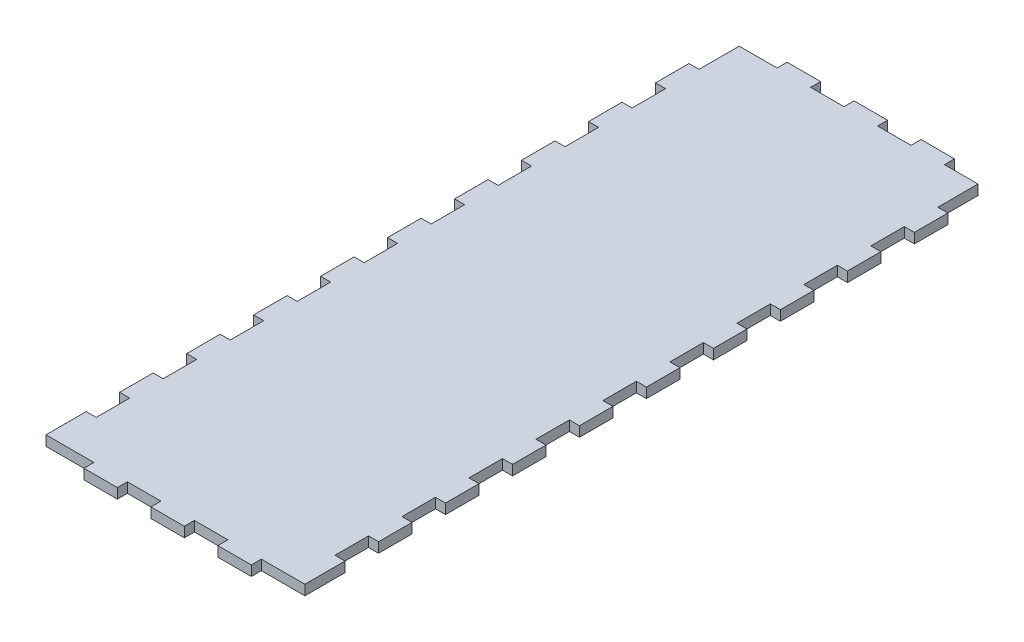
SolidWorks part; units mm, degrees
ref_plane "Front Plane" through (0, 0, 0) normal (0, 0, 1) x (1, 0, 0)
ref_plane "Top Plane" through (0, 0, 0) normal (0, 1, 0) x (1, 0, 0)
ref_plane "Right Plane" through (0, 0, 0) normal (1, 0, 0) x (0, 0, -1)
sketch "Sketch1" plane through (0, 0, 0) normal (0, 1, 0) x (1, 0, 0)
  line L1 (0, 0) -> (35.65, 0)
  line L2 (0, 0) -> (0, 204)
  line L3 (0, 204) -> (35.65, 204)
  line L4 (35.65, 0) -> (35.65, 204)
  dimension "D1" = 35.65
  dimension "D2" = 204
extrude "Boss-Extrude1" add sketch "Sketch1" along normal blind 3
sketch "Sketch2" plane through (35.65, 0, 0) normal (1, 0, 0) x (0, 0, -1)
  line L0 (0, 3) -> (204, 3) construction
  line L1 (0, 0) -> (12, 0)
  line L2 (0, 0) -> (0, 3)
  line L3 (0, 3) -> (12, 3)
  line L4 (12, 0) -> (12, 3)
  line L5 (0, 0) -> (204, 0) construction
  line L6 (22, 0) -> (32, 0)
  line L7 (22, 0) -> (22, 3)
  line L8 (22, 3) -> (32, 3)
  line L9 (32, 0) -> (32, 3)
  line L10 (42, 0) -> (42, 3)
  line L11 (42, 0) -> (52, 0)
  line L12 (52, 0) -> (52, 3)
  line L13 (42, 3) -> (52, 3)
  line L14 (62, 0) -> (62, 3)
  line L15 (62, 0) -> (72, 0)
  line L16 (72, 0) -> (72, 3)
  line L17 (62, 3) -> (72, 3)
  line L18 (82, 0) -> (82, 3)
  line L19 (82, 0) -> (92, 0)
  line L20 (92, 0) -> (92, 3)
  line L21 (82, 3) -> (92, 3)
  line L22 (102, 0) -> (102, 3)
  line L23 (102, 0) -> (112, 0)
  line L24 (112, 0) -> (112, 3)
  line L25 (102, 3) -> (112, 3)
  line L26 (122, 0) -> (122, 3)
  line L27 (122, 0) -> (132, 0)
  line L28 (132, 0) -> (132, 3)
  line L29 (122, 3) -> (132, 3)
  line L30 (142, 0) -> (142, 3)
  line L31 (142, 0) -> (152, 0)
  line L32 (152, 0) -> (152, 3)
  line L33 (142, 3) -> (152, 3)
  line L34 (162, 0) -> (162, 3)
  line L35 (162, 0) -> (172, 0)
  line L36 (172, 0) -> (172, 3)
  line L37 (162, 3) -> (172, 3)
  line L38 (182, 0) -> (182, 3)
  line L39 (182, 0) -> (192, 0)
  line L40 (192, 0) -> (192, 3)
  line L41 (182, 3) -> (192, 3)
  dimension "D1" = 12
  dimension "D2" = 10
  dimension "D3" = 10
  dimension "D4" = 9
extrude "Boss-Extrude2" add sketch "Sketch2" along normal blind 3
mirror "Mirror1" about plane through (0, 0, 0) normal (1, 0, 0) of "Boss-Extrude2", "Boss-Extrude1"
sketch "Esquisse1" plane through (0, 0, -204) normal (0, 0, -1) x (-1, 0, 0)
  line L0 (-35.65, 0) -> (35.65, 0) construction
  line L1 (-25.65, 0) -> (-15.65, 0)
  line L2 (-25.65, 0) -> (-25.65, 3)
  line L3 (-25.65, 3) -> (-15.65, 3)
  line L4 (-15.65, 0) -> (-15.65, 3)
  line L5 (-35.65, 3) -> (35.65, 3) construction
  line L6 (-35.65, 3) -> (-35.65, 0) construction
  line L7 (-5.65, 0) -> (4.35, 0)
  line L8 (-5.65, 0) -> (-5.65, 3)
  line L9 (-5.65, 3) -> (4.35, 3)
  line L10 (4.35, 0) -> (4.35, 3)
  line L11 (14.35, 0) -> (24.35, 0)
  line L12 (14.35, 0) -> (14.35, 3)
  line L13 (14.35, 3) -> (24.35, 3)
  line L14 (24.35, 0) -> (24.35, 3)
  dimension "D1" = 10
  dimension "D2" = 10
  dimension "D4" = 10
  dimension "D3" = 3
extrude "Boss.-Extru.1" add sketch "Esquisse1" along normal blind 3
sketch "Esquisse2" plane through (0, 0, 0) normal (0, 0, 1) x (1, 0, 0)
  line L0 (-38.65, 0) -> (38.65, 0) construction
  line L1 (-24.35, 0) -> (-14.35, 0)
  line L2 (-24.35, 0) -> (-24.35, 3)
  line L3 (-24.35, 3) -> (-14.35, 3)
  line L4 (-14.35, 0) -> (-14.35, 3)
  line L5 (-38.65, 3) -> (38.65, 3) construction
  line L7 (-4.35, 0) -> (5.65, 0)
  line L8 (-4.35, 0) -> (-4.35, 3)
  line L9 (-4.35, 3) -> (5.65, 3)
  line L10 (5.65, 0) -> (5.65, 3)
  line L11 (15.65, 0) -> (25.65, 0)
  line L12 (15.65, 0) -> (15.65, 3)
  line L13 (15.65, 3) -> (25.65, 3)
  line L14 (25.65, 0) -> (25.65, 3)
  line L16 (38.65, 3) -> (38.65, 0) construction
  dimension "D1" = 10
  dimension "D2" = 13
  dimension "D4" = 10
  dimension "D3" = 3
extrude "Boss.-Extru.2" add sketch "Esquisse2" along normal blind 3
